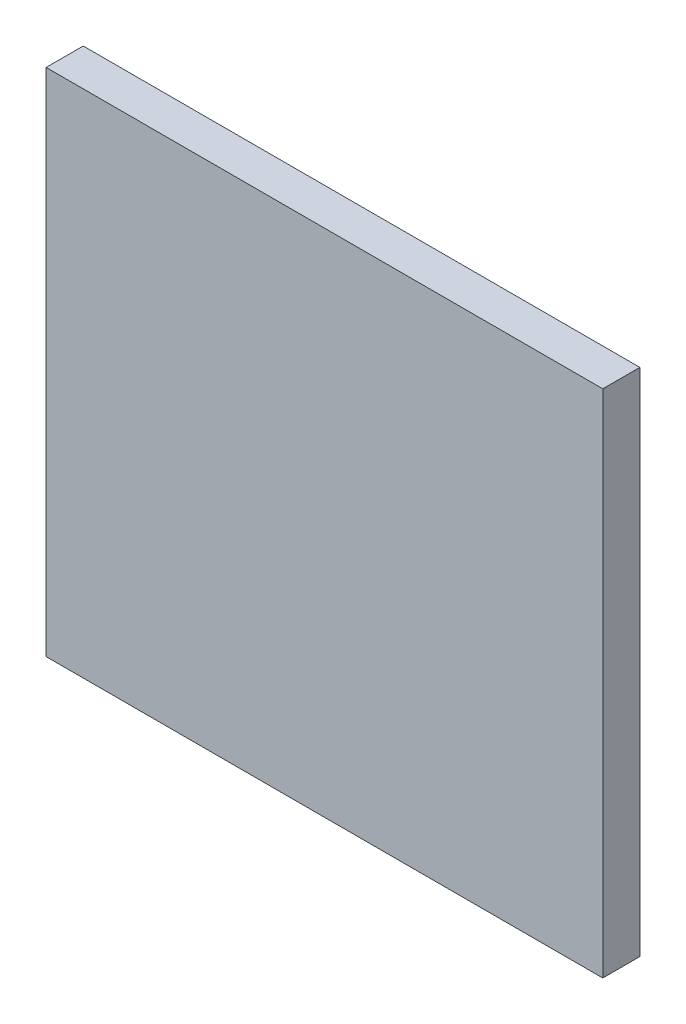
SolidWorks part; units mm, degrees
material "Gomma"
ref_plane "Piano frontale" through (0, 0, 0) normal (0, 0, 1) x (1, 0, 0)
ref_plane "Piano superiore" through (0, 0, 0) normal (0, 1, 0) x (1, 0, 0)
ref_plane "Piano destro" through (0, 0, 0) normal (1, 0, 0) x (0, 0, -1)
sketch "Schizzo2" plane through (0, 0, 0) normal (0, 0, 1) x (1, 0, 0)
  line L1 (6, -5.5) -> (-6, -5.5)
  line L2 (6, -5.5) -> (6, 5.5)
  line L3 (6, 5.5) -> (-6, 5.5)
  line L4 (-6, -5.5) -> (-6, 5.5)
  line L5 (6, -5.5) -> (-6, 5.5) construction
  line L6 (6, 5.5) -> (-6, -5.5) construction
  point P0 (0, 0)
  dimension "D1" = 12
  dimension "D2" = 11
extrude "Estrusione-Estrusione1" add sketch "Schizzo2" along normal blind 0.8
